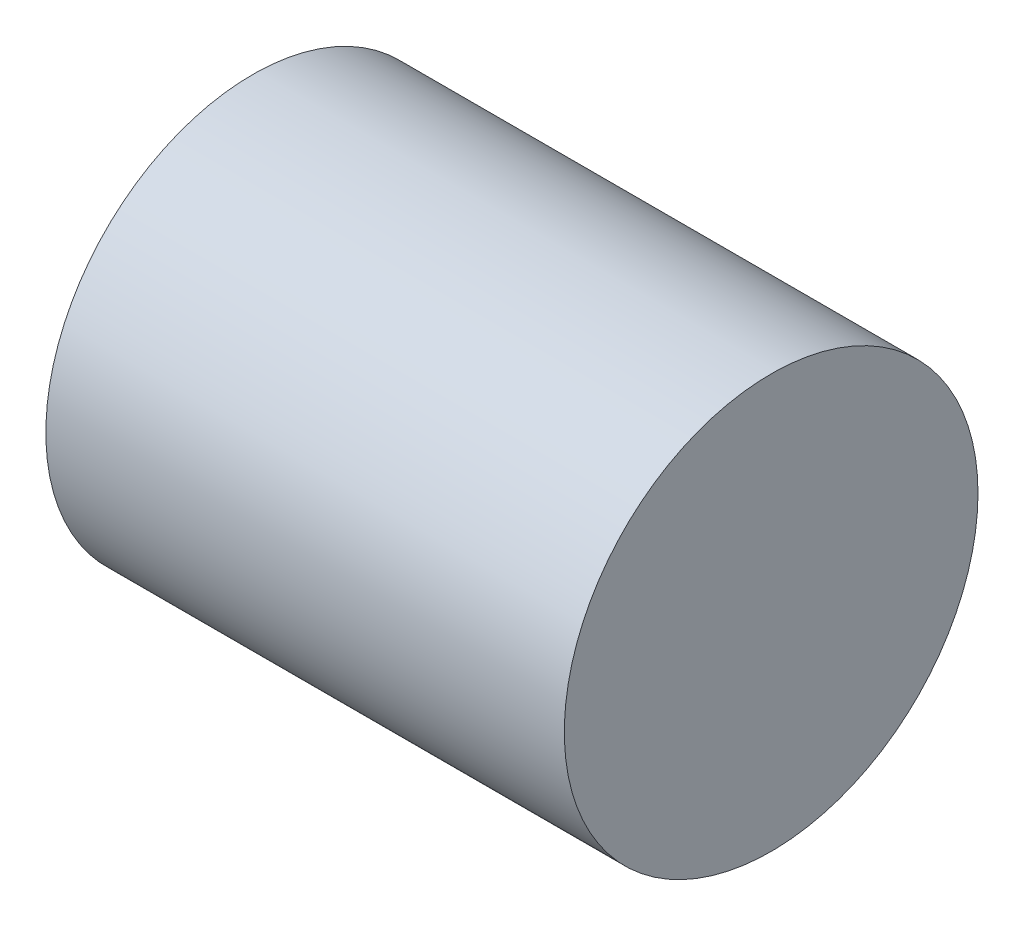
SolidWorks part; units mm, degrees
ref_plane "Front Plane" through (0, 0, 0) normal (0, 0, 1) x (1, 0, 0)
ref_plane "Top Plane" through (0, 0, 0) normal (0, 1, 0) x (1, 0, 0)
ref_plane "Right Plane" through (0, 0, 0) normal (1, 0, 0) x (0, 0, -1)
sketch "Sketch1" plane through (0, 0, 0) normal (1, 0, 0) x (0, 0, -1)
  circle A0 centre (0, 0) radius 0.7979
extrude "Boss-Extrude1" add sketch "Sketch1" along normal blind 2
